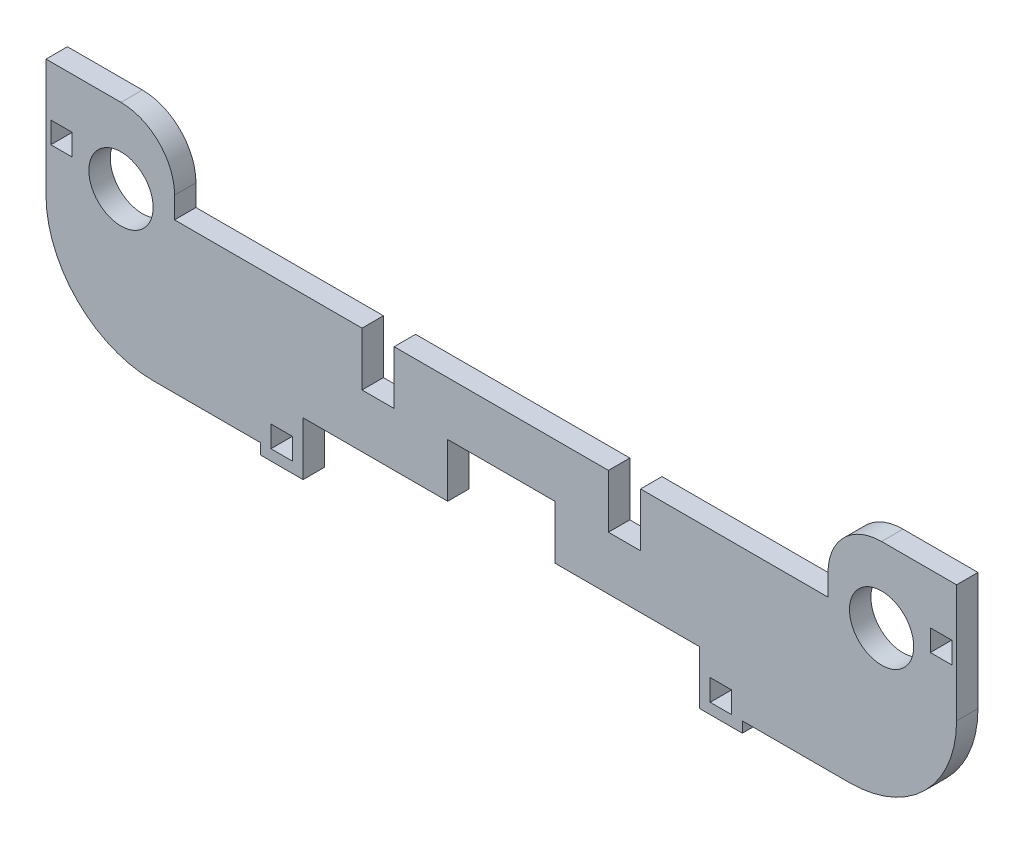
SolidWorks part; units mm, degrees
ref_plane "Front Plane" through (0, 0, 0) normal (0, 0, 1) x (1, 0, 0)
ref_plane "Top Plane" through (0, 0, 0) normal (0, 1, 0) x (1, 0, 0)
ref_plane "Right Plane" through (0, 0, 0) normal (1, 0, 0) x (0, 0, -1)
sketch "Sketch1" plane through (0, 0, 0) normal (0, 0, 1) x (1, 0, 0)
  line L0 (-35.5, -5) -> (35.5, 5) construction
  line L1 (-35.5, -5) -> (35.5, -5)
  line L2 (-35.5, -5) -> (-35.5, 5)
  line L3 (-35.5, 5) -> (-13, 5)
  line L4 (35.5, -5) -> (35.5, 5)
  line L5 (35.5, -5) -> (0, 0) construction
  line L6 (0, 0) -> (-35.5, 5) construction
  line L7 (-13, 5) -> (-13, 0)
  line L8 (-13, 0) -> (13, 0)
  line L9 (13, 0) -> (13, 5)
  line L10 (13, 5) -> (35.5, 5)
  line L11 (0, 0) -> (0, -5) construction
  line L12 (-35.5, 0) -> (-42.5, 0)
  line L13 (-42.5, 0) -> (-42.5, 12)
  line L14 (-42.5, 12) -> (-30.5, 12)
  line L15 (-30.5, 12) -> (-30.5, 5)
  line L16 (35.5, 0) -> (42.5, 0)
  line L17 (-42.05, 5.3) -> (-40.05, 5.3)
  line L18 (-42.05, 5.3) -> (-42.05, 7.3)
  line L19 (-42.05, 7.3) -> (-40.05, 7.3)
  line L20 (-40.05, 5.3) -> (-40.05, 7.3)
  line L21 (42.5, 0) -> (42.5, 12)
  line L22 (42.05, 7.3) -> (40.05, 7.3)
  line L23 (42.05, 5.3) -> (42.05, 7.3)
  line L24 (42.05, 5.3) -> (40.05, 5.3)
  line L25 (40.05, 5.3) -> (40.05, 7.3)
  line L26 (30.5, 12) -> (30.5, 5)
  line L27 (42.5, 12) -> (30.5, 12)
  line L28 (-5, -5) -> (-5, 0)
  line L29 (-5, 0) -> (5, 0)
  line L30 (5, 0) -> (5, -5)
  line L31 (0, 0) -> (0, -5) construction
  line L32 (-10, 0) -> (-10, 5)
  line L33 (-10, 5) -> (10, 5)
  line L34 (10, 5) -> (10, 0)
  line L35 (10, 0) -> (-10, 0)
  line L36 (0, 5) -> (0, 0) construction
  line L37 (18.5, -9) -> (18.5, -5)
  line L38 (-18.5, -9) -> (-18.5, -5)
  line L39 (-22.5, -9) -> (-22.5, -10)
  line L40 (21.5, -7) -> (19.5, -7)
  line L41 (21.5, -7) -> (21.5, -9)
  line L42 (21.5, -9) -> (19.5, -9)
  line L43 (19.5, -7) -> (19.5, -9)
  line L44 (-22.5, -10) -> (-18.5, -10)
  line L45 (-18.5, -10) -> (-18.5, -9)
  line L46 (-19.5, -7) -> (-19.5, -9)
  line L47 (42.5, -9) -> (22.5, -9)
  line L48 (22.5, -9) -> (22.5, -10)
  line L49 (22.5, -10) -> (18.5, -10)
  line L50 (18.5, -10) -> (18.5, -9)
  line L51 (35.5, -5) -> (42.5, -5)
  line L52 (42.5, -5) -> (42.5, 0)
  line L53 (-42.5, 0) -> (-42.5, -5)
  line L54 (-42.5, -5) -> (-35.5, -5)
  line L55 (-42.5, -5) -> (-42.5, -9)
  line L56 (-21.5, -7) -> (-19.5, -7)
  line L57 (42.5, -5) -> (42.5, -9)
  line L58 (-21.5, -7) -> (-21.5, -9)
  line L59 (-21.5, -9) -> (-19.5, -9)
  line L60 (-42.5, -9) -> (-22.5, -9)
  circle A0 centre (-35.5, 5) radius 3
  circle A1 centre (35.5, 5) radius 3
  dimension "D5" = 6
  dimension "D6" = 0
  dimension "D22" = 5
  dimension "D23" = 6
  dimension "D1" = 10
  dimension "D2" = 71
  dimension "D3" = 5
  dimension "D4" = 26
  dimension "D7" = 7
  dimension "D8" = 4.7
  dimension "D9" = 0.45
  dimension "D10" = 2
  dimension "D11" = 10
  dimension "D12" = 5
  dimension "D13" = 20
  dimension "D14" = 24
  dimension "D15" = 4
  dimension "D16" = 2
  dimension "D17" = 4
  dimension "D18" = 1
  dimension "D19" = 1
  dimension "D20" = 1
  dimension "D21" = 5
  dimension "D24" = 0
extrude "Boss-Extrude2" add sketch "Sketch1" along normal blind 2 contours A0 L3 L15 L14 L13 L12 L2 L20 L17 L18 L19 | L55 L60 L39 L44 L45 L38 L1 L54 L59 L58 L56 L46 | L53 L54 L2 L12 | A0 L2 L1 L28 L8 L7 L3 | L34 L33 L32 L8 | L57 L51 L1 L37 L50 L49 L48 L47 L43 L40 L41 L42 | L51 L52 L16 L4 | A1 L4 L16 L21 L27 L26 L10 L24 L25 L22 L23 | A1 L10 L9 L8 L30 L1 L4
fillet "Fillet1" radius 10 1 edges at (-42.5, -9, 1)
fillet "Fillet2" radius 10 1 edges at (42.5, -9, 1)
fillet "Fillet3" radius 5 1 edges at (-30.5, 12, 1)
fillet "Fillet4" radius 5 1 edges at (30.5, 12, 1)
